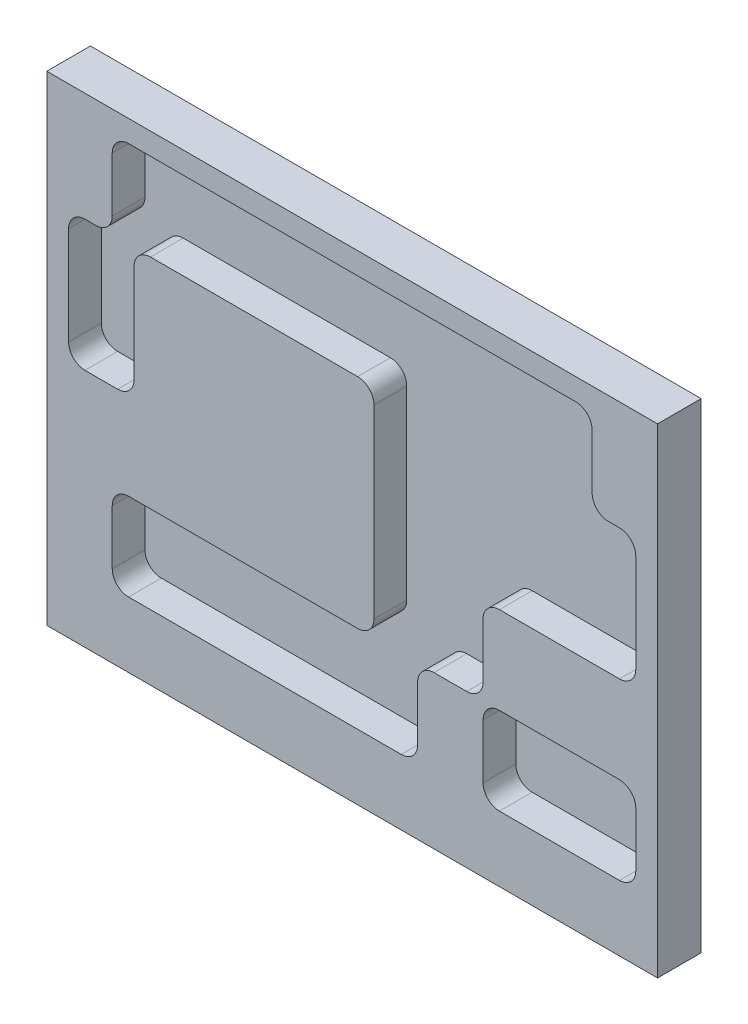
SolidWorks part; units mm, degrees
ref_plane "Front Plane" through (0, 0, 0) normal (0, 0, 1) x (1, 0, 0)
ref_plane "Top Plane" through (0, 0, 0) normal (0, 1, 0) x (1, 0, 0)
ref_plane "Right Plane" through (0, 0, 0) normal (1, 0, 0) x (0, 0, -1)
sketch "Sketch1" plane through (0, 0, 0) normal (0, 0, 1) x (1, 0, 0)
  line L1 (-88.9, 69.85) -> (88.9, 69.85)
  line L2 (-88.9, 69.85) -> (-88.9, -69.85)
  line L3 (-88.9, -69.85) -> (88.9, -69.85)
  line L4 (88.9, 69.85) -> (88.9, -69.85)
  line L5 (-88.9, 69.85) -> (88.9, -69.85) construction
  line L6 (-88.9, -69.85) -> (88.9, 69.85) construction
  point P0 (0, 0)
  dimension "D1" = 139.7
  dimension "D2" = 177.8
extrude "Boss-Extrude1" add sketch "Sketch1" along normal blind 12.7
sketch "Sketch2" plane through (0, 0, 12.7) normal (0, 0, 1) x (1, 0, 0)
  line L0 (88.9, 69.85) -> (-88.9, 69.85) construction
  line L1 (-65.0875, 63.5) -> (65.0875, 63.5)
  line L2 (-69.85, 58.7375) -> (-69.85, 42.8625)
  line L3 (-58.7375, 38.1) -> (1.5875, 38.1)
  line L4 (69.85, 58.7375) -> (69.85, 42.8625)
  line L5 (-69.85, 63.5) -> (69.85, 38.1) construction
  line L6 (-69.85, 38.1) -> (69.85, 63.5) construction
  line L7 (88.9, -69.85) -> (88.9, 69.85) construction
  line L8 (0, 50.8) -> (0, 0) construction
  line L9 (-88.9, 69.85) -> (-88.9, -69.85) construction
  line L10 (74.6125, 38.1) -> (77.7875, 38.1)
  line L11 (6.35, 33.3375) -> (6.35, 0)
  line L12 (42.8625, 0) -> (77.7875, 0)
  line L13 (82.55, 33.3375) -> (82.55, 4.7625)
  line L14 (-74.6125, 38.1) -> (-77.7875, 38.1)
  line L15 (-63.5, 33.3375) -> (-63.5, 4.7625)
  line L16 (-68.2625, 0) -> (-77.7875, 0)
  line L17 (-82.55, 33.3375) -> (-82.55, 4.7625)
  line L18 (-63.5, 0) -> (6.35, 0) construction
  line L19 (-69.85, 38.1) -> (-63.5, 38.1) construction
  line L20 (6.35, 38.1) -> (69.85, 38.1) construction
  line L21 (14.2875, -50.8) -> (42.8625, -50.8) construction
  line L22 (42.8625, -25.4) -> (77.7875, -25.4)
  line L23 (38.1, -30.1625) -> (38.1, -46.0375)
  line L24 (42.8625, -50.8) -> (77.7875, -50.8)
  line L25 (82.55, -30.1625) -> (82.55, -46.0375)
  line L26 (38.1, -25.4) -> (82.55, -50.8) construction
  line L27 (38.1, -50.8) -> (82.55, -25.4) construction
  line L28 (-65.0875, -25.4) -> (1.5875, -25.4)
  line L29 (-69.85, -30.1625) -> (-69.85, -46.0375)
  line L30 (-65.0875, -50.8) -> (14.2875, -50.8)
  line L31 (19.05, -30.1625) -> (19.05, -46.0375)
  line L32 (-69.85, -25.4) -> (19.05, -50.8) construction
  line L33 (-69.85, -50.8) -> (19.05, -25.4) construction
  line L34 (38.1, -25.4) -> (19.05, -25.4) construction
  line L35 (-88.9, -69.85) -> (88.9, -69.85) construction
  line L36 (19.05, -25.4) -> (1.5875, -25.4) construction
  line L38 (38.1, -4.7625) -> (38.1, -20.6375)
  line L39 (33.3375, -25.4) -> (23.8125, -25.4)
  line L40 (6.35, 0) -> (6.35, -20.6375)
  arc A0 (65.0875, 63.5) -> (69.85, 58.7375) centre (65.0875, 58.7375) cw
  arc A1 (74.6125, 38.1) -> (69.85, 42.8625) centre (74.6125, 42.8625) cw
  arc A2 (77.7875, 38.1) -> (82.55, 33.3375) centre (77.7875, 33.3375) cw
  arc A3 (77.7875, 0) -> (82.55, 4.7625) centre (77.7875, 4.7625) ccw
  arc A4 (42.8625, 0) -> (38.1, -4.7625) centre (42.8625, -4.7625) ccw
  arc A5 (1.5875, 38.1) -> (6.35, 33.3375) centre (1.5875, 33.3375) cw
  arc A6 (-77.7875, 38.1) -> (-82.55, 33.3375) centre (-77.7875, 33.3375) ccw
  arc A7 (-63.5, 4.7625) -> (-68.2625, 0) centre (-68.2625, 4.7625) cw
  arc A8 (-77.7875, 0) -> (-82.55, 4.7625) centre (-77.7875, 4.7625) cw
  arc A9 (-65.0875, 63.5) -> (-69.85, 58.7375) centre (-65.0875, 58.7375) ccw
  arc A10 (-58.7375, 38.1) -> (-63.5, 33.3375) centre (-58.7375, 33.3375) ccw
  arc A11 (-69.85, 42.8625) -> (-74.6125, 38.1) centre (-74.6125, 42.8625) cw
  arc A12 (77.7875, -25.4) -> (82.55, -30.1625) centre (77.7875, -30.1625) cw
  arc A13 (77.7875, -50.8) -> (82.55, -46.0375) centre (77.7875, -46.0375) ccw
  arc A14 (38.1, -46.0375) -> (42.8625, -50.8) centre (42.8625, -46.0375) ccw
  arc A15 (42.8625, -25.4) -> (38.1, -30.1625) centre (42.8625, -30.1625) ccw
  arc A16 (19.05, -30.1625) -> (23.8125, -25.4) centre (23.8125, -30.1625) cw
  arc A17 (14.2875, -50.8) -> (19.05, -46.0375) centre (14.2875, -46.0375) ccw
  arc A18 (-69.85, -46.0375) -> (-65.0875, -50.8) centre (-65.0875, -46.0375) ccw
  arc A19 (-65.0875, -25.4) -> (-69.85, -30.1625) centre (-65.0875, -30.1625) ccw
  arc A20 (1.5875, -25.4) -> (6.35, -20.6375) centre (1.5875, -20.6375) ccw
  arc A21 (33.3375, -25.4) -> (38.1, -20.6375) centre (33.3375, -20.6375) ccw
  point P0 (0, 50.8)
  point P32 (82.55, 0)
  point P55 (60.325, -38.1)
  point P60 (-25.4, -38.1)
  dimension "D9" = 4.7625
  dimension "D16" = 4.7625
  dimension "D19" = 4.7625
  dimension "D20" = 4.7625
  dimension "D1" = 6.35
  dimension "D2" = 19.05
  dimension "D3" = 25.4
  dimension "D4" = 6.35
  dimension "D5" = 76.2
  dimension "D6" = 69.85
  dimension "D7" = 6.35
  dimension "D8" = 25.4
  dimension "D10" = 25.4
  dimension "D11" = 6.35
  dimension "D12" = 19.05
  dimension "D13" = 50.8
  dimension "D14" = 69.85
  dimension "D15" = 158.75
  dimension "D17" = 50.8
  dimension "D18" = 95.25
extrude "Cut-Extrude1" cut sketch "Sketch2" against normal blind 9.525
